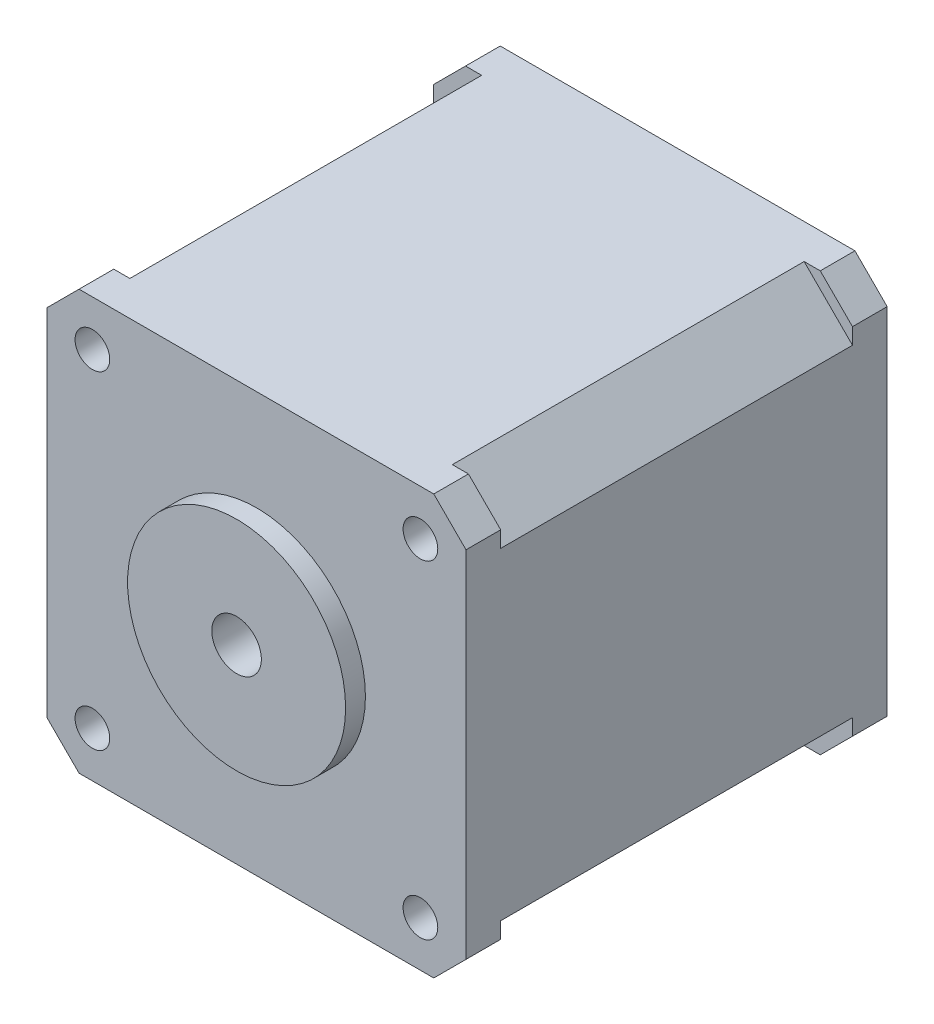
SolidWorks part; units mm, degrees
ref_plane "Front Plane" through (0, 0, 0) normal (0, 0, 1) x (1, 0, 0)
ref_plane "Top Plane" through (0, 0, 0) normal (0, 1, 0) x (1, 0, 0)
ref_plane "Right Plane" through (0, 0, 0) normal (1, 0, 0) x (0, 0, -1)
sketch "Sketch1" plane through (0, 0, 0) normal (0, 0, 1) x (1, 0, 0)
  line L1 (21.15, -21.15) -> (-21.15, -21.15)
  line L2 (21.15, -21.15) -> (21.15, 21.15)
  line L3 (21.15, 21.15) -> (-21.15, 21.15)
  line L4 (-21.15, -21.15) -> (-21.15, 21.15)
  line L5 (21.15, -21.15) -> (-21.15, 21.15) construction
  line L6 (21.15, 21.15) -> (-21.15, -21.15) construction
  point P0 (0, 0)
  dimension "D1" = 42.3
  dimension "D2" = 42.3
extrude "Boss-Extrude1" add sketch "Sketch1" along normal blind 42.5
sketch "Sketch2" plane through (0, 0, 42.5) normal (0, 0, 1) x (1, 0, 0)
  circle A0 centre (0, 0) radius 11
  dimension "D1" = 22
extrude "Boss-Extrude2" add sketch "Sketch2" along normal blind 2
sketch "Sketch3" plane through (0, 0, 42.5) normal (0, 0, 1) x (1, 0, 0)
  line L1 (16.55, -16.55) -> (-16.55, -16.55) construction
  line L2 (16.55, -16.55) -> (16.55, 16.55) construction
  line L3 (16.55, 16.55) -> (-16.55, 16.55) construction
  line L4 (-16.55, -16.55) -> (-16.55, 16.55) construction
  line L5 (16.55, -16.55) -> (-16.55, 16.55) construction
  line L6 (16.55, 16.55) -> (-16.55, -16.55) construction
  circle A0 centre (-16.55, 16.55) radius 1.75
  circle A1 centre (16.55, 16.55) radius 1.75
  circle A2 centre (16.55, -16.55) radius 1.75
  circle A3 centre (-16.55, -16.55) radius 1.75
  point P0 (0, 0)
  point P16 (0, 0)
  dimension "D3" = 3.5
  dimension "D1" = 33.1
  dimension "D2" = 33.1
  dimension "D4" = 4
extrude "Cut-Extrude1" cut sketch "Sketch3" against normal through all
sketch "Sketch4" plane through (0, 0, 42.5) normal (0, 0, 1) x (1, 0, 0)
  line L0 (-16.55, 16.55) -> (-21.15, 21.15) construction
  line L1 (-21.15, 17.8973) -> (-21.15, 21.15)
  line L2 (-21.15, 21.15) -> (-17.8973, 21.15)
  line L3 (-17.8973, 21.15) -> (-21.15, 17.8973)
  line L4 (17.8973, 21.15) -> (21.15, 21.15)
  line L5 (21.15, 21.15) -> (21.15, 17.8973)
  line L6 (21.15, 17.8973) -> (17.8973, 21.15)
  line L7 (21.15, -17.8973) -> (21.15, -21.15)
  line L8 (21.15, -21.15) -> (17.8973, -21.15)
  line L9 (17.8973, -21.15) -> (21.15, -17.8973)
  line L10 (-17.8973, -21.15) -> (-21.15, -21.15)
  line L11 (-21.15, -21.15) -> (-21.15, -17.8973)
  line L12 (-21.15, -17.8973) -> (-17.8973, -21.15)
  circle A0 centre (-21.15, 21.15) radius 3.2527 construction
  point P3 (-18.85, 18.85)
  point P20 (0, 0)
  dimension "D1" = 4
extrude "Cut-Extrude2" cut sketch "Sketch4" against normal through all
sketch "Sketch5" plane through (0, 0, 44.5) normal (0, 0, 1) x (1, 0, 0)
  circle A0 centre (0, 0) radius 2.5
  dimension "D1" = 5
ref_plane "Plane1" through (0, 0, 7.5) normal (0, 0, 1) x (1, 0, 0)
extrude "Cut-Extrude3" cut sketch "Sketch5" against normal through all
sketch "Sketch6" plane through (0, 0, 44.5) normal (0, 0, 1) x (1, 0, 0)
  circle A0 centre (0, 0) radius 2.5
  dimension "D1" = 5
extrude "Boss-Extrude3" add sketch "Sketch6" along normal blind 22 and the other way blind 47.5
sketch "Sketch7" plane through (0, 0, 0) normal (0, 0, -1) x (-1, 0, 0)
  circle A0 centre (0, 0) radius 5
  circle A1 centre (0, 0) radius 2.5
  dimension "D1" = 10
extrude "Cut-Extrude4" cut sketch "Sketch7" against normal blind 5
sketch "Sketch8" plane through (0, 0, 66.5) normal (0, 0, 1) x (1, 0, 0)
  line L0 (2.5, 0) -> (0, 2.5)
  arc A0 (2.5, 0) -> (0, 2.5) centre (0, 0) ccw
extrude "Cut-Extrude5" cut sketch "Sketch8" against normal blind 20
sketch "Sketch9" plane through (0, 0, 66.5) normal (0, 0, 1) x (1, 0, 0)
  circle A0 centre (0, 0) radius 2.5
  dimension "D1" = 5
extrude "Cut-Extrude6" cut sketch "Sketch9" against normal through all
ref_plane "Plane2" through (0, 0, 3.5) normal (0, 0, 1) x (1, 0, 0)
sketch "Sketch10" plane through (0, 0, 3.5) normal (0, 0, 1) x (1, 0, 0)
  line L1 (25, -25) -> (12.421, -25)
  line L2 (25, -25) -> (25, -12.421)
  line L3 (25, 25) -> (12.421, 25)
  line L4 (-25, -25) -> (-25, -12.421)
  line L5 (25, -25) -> (19.5237, -19.5237) construction
  line L6 (25, 25) -> (19.5237, 19.5237) construction
  line L7 (17.8973, -19.5237) -> (-17.8973, -19.5237) construction
  line L8 (19.5237, -17.8973) -> (19.5237, 17.8973) construction
  line L9 (17.8973, 19.5237) -> (-17.8973, 19.5237) construction
  line L10 (-19.5237, -17.8973) -> (-19.5237, 17.8973) construction
  line L11 (18.7105, -18.7105) -> (-18.7105, 18.7105) construction
  line L12 (18.7105, 18.7105) -> (-18.7105, -18.7105) construction
  line L13 (-21.15, 17.8973) -> (-17.8973, 21.15) construction
  line L14 (-19.5237, 17.8973) -> (-17.8973, 19.5237) construction
  line L15 (17.8973, 19.5237) -> (19.5237, 17.8973) construction
  line L16 (19.5237, -17.8973) -> (17.8973, -19.5237) construction
  line L17 (-17.8973, -19.5237) -> (-19.5237, -17.8973) construction
  line L18 (-19.5237, 19.5237) -> (-25, 25) construction
  line L19 (18.7105, 18.7105) -> (-18.7105, -18.7105) construction
  line L20 (18.7105, -18.7105) -> (-18.7105, 18.7105) construction
  line L21 (-19.5237, -19.5237) -> (-25, -25) construction
  line L22 (-12.421, -25) -> (-25, -12.421)
  line L23 (25, -12.421) -> (12.421, -25)
  line L24 (25, 12.421) -> (12.421, 25)
  line L25 (-25, 12.421) -> (-25, 25)
  line L26 (-12.421, 25) -> (-25, 25)
  line L27 (25, 12.421) -> (25, 25)
  line L28 (-12.421, -25) -> (-25, -25)
  line L29 (-25, 12.421) -> (-12.421, 25)
  point P0 (0, 0)
  point P5 (0, 0)
  point P24 (0, 0)
  point P29 (-18.7105, 18.7105)
  point P32 (-18.7105, -18.7105)
  point P35 (18.7105, -18.7105)
  point P38 (18.7105, 18.7105)
  dimension "D1" = 4
  dimension "D2" = 50
  dimension "D3" = 39.0473
extrude "Cut-Extrude7" cut sketch "Sketch10" along normal blind 35.5
